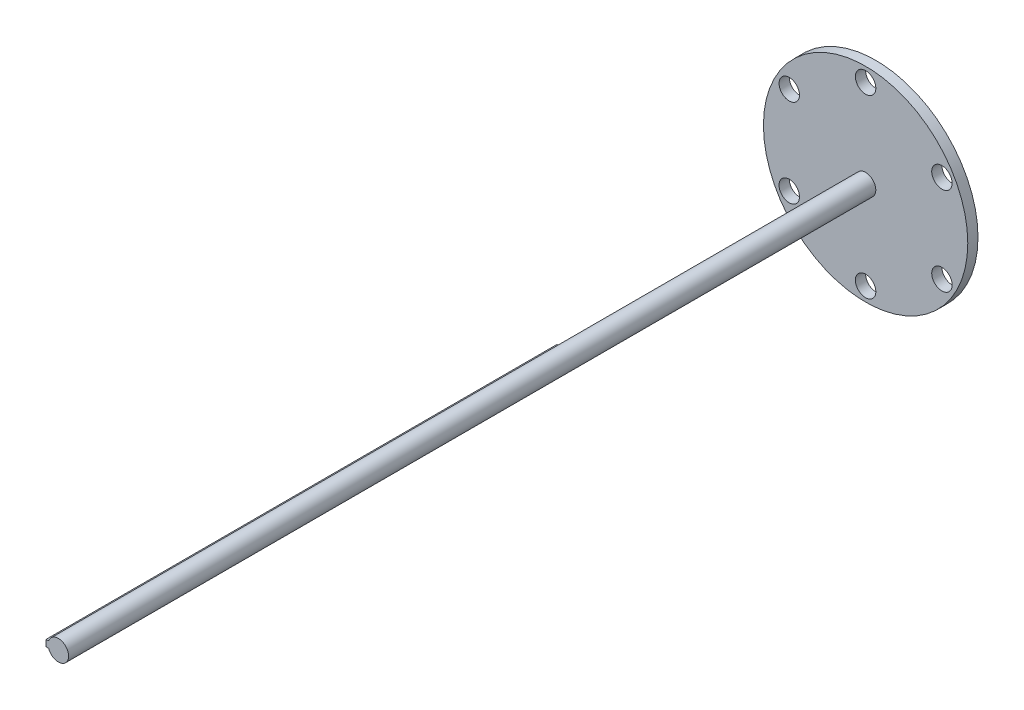
SolidWorks part; units mm, degrees
ref_plane "前视基准面" through (0, 0, 0) normal (0, 0, 1) x (1, 0, 0)
ref_plane "上视基准面" through (0, 0, 0) normal (0, 1, 0) x (1, 0, 0)
ref_plane "右视基准面" through (0, 0, 0) normal (1, 0, 0) x (0, 0, -1)
other "Configuration Table"
sketch "草图1" plane through (0, 0, 0) normal (0, 0, 1) x (1, 0, 0)
  circle A0 centre (0, 0) radius 2
extrude "凸台-拉伸1" add sketch "草图1" along normal blind 160
sketch "草图3" plane through (0, 0, 0) normal (0, 0, -1) x (-1, 0, 0)
  circle A0 centre (0, 0) radius 20
extrude "凸台-拉伸2" add sketch "草图3" against normal blind 2
sketch "草图4" plane through (0, 0, 0) normal (0, 0, -1) x (-1, 0, 0)
  circle A0 centre (0, 17.25) radius 2
  circle A1 centre (14.9389, 8.625) radius 2
  circle A2 centre (14.9389, -8.625) radius 2
  circle A3 centre (0, -17.25) radius 2
  circle A4 centre (-14.9389, -8.625) radius 2
  circle A5 centre (-14.9389, 8.625) radius 2
  point P15 (0, 0)
  dimension "D1" = 17.25
  dimension "D2" = 6
extrude "切除-拉伸1" cut sketch "草图4" against normal blind 2
sketch "草图5" plane through (0, 0, 160) normal (0, 0, 1) x (1, 0, 0)
  line L0 (-2, 0) -> (1.8112, 0) construction
  line L1 (-2.4198, 0) -> (-2.4198, 0.625)
  line L2 (-2.4198, 0.625) -> (-1.8998, 0.625)
  line L3 (-2.4198, 0) -> (-2.4198, -0.625)
  line L4 (-2.4198, -0.625) -> (-1.8998, -0.625)
  line L5 (-1.8998, 0.625) -> (-1.8998, -0.625)
  circle A0 centre (0, 0) radius 2 construction
  circle A1 centre (0, 0) radius 2 construction
  dimension "D1" = 0.625
  dimension "D2" = 0.625
  dimension "D3" = 0.52
extrude "凸台-拉伸3" add sketch "草图5" against normal blind 100
